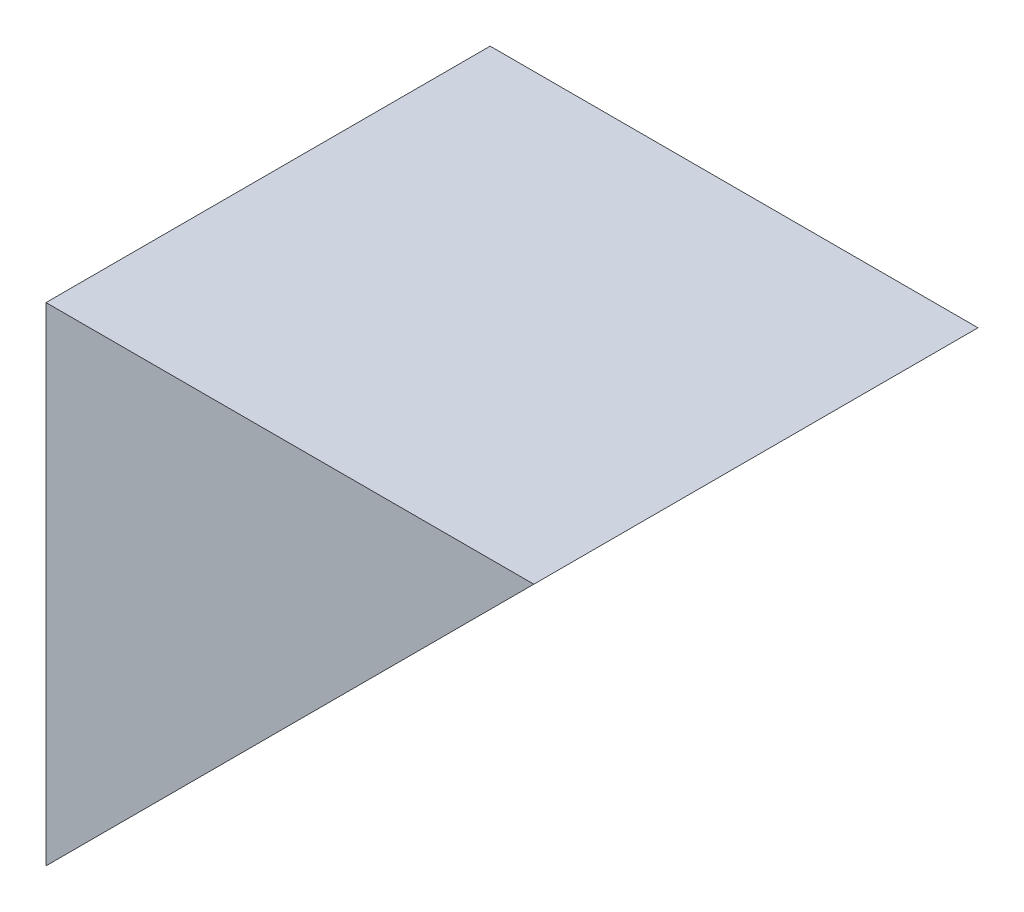
SolidWorks part; units mm, degrees
ref_plane "Front Plane" through (0, 0, 0) normal (0, 0, 1) x (1, 0, 0)
ref_plane "Top Plane" through (0, 0, 0) normal (0, 1, 0) x (1, 0, 0)
ref_plane "Right Plane" through (0, 0, 0) normal (1, 0, 0) x (0, 0, -1)
sketch "Sketch1" plane through (0, 0, 0) normal (0, 0, 1) x (1, 0, 0)
  line L0 (0, 0) -> (189.992, 189.992)
  line L2 (0, 0) -> (0, 189.992)
  line L3 (0, 189.992) -> (189.992, 189.992)
  dimension "D1" = 189.992
extrude "Boss-Extrude1" add sketch "Sketch1" along normal blind 172.974
